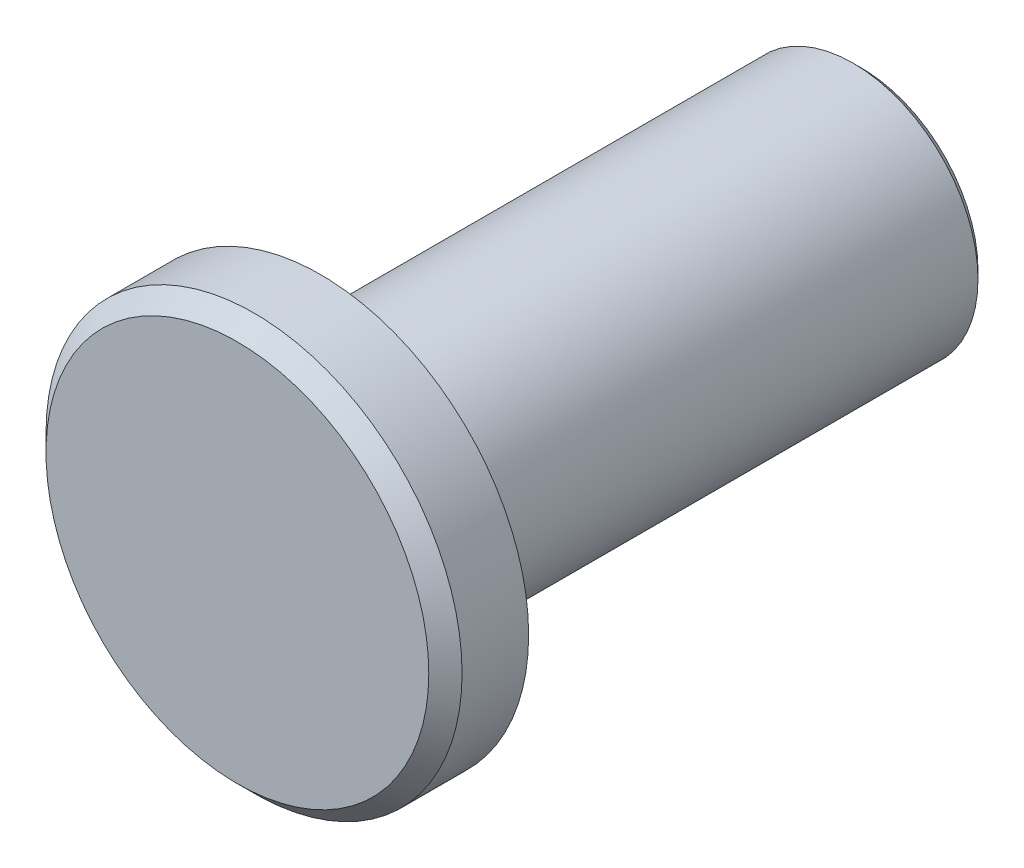
SolidWorks part; units mm, degrees
material "Brass"
ref_plane "Front Plane" through (0, 0, 0) normal (0, 0, 1) x (1, 0, 0)
ref_plane "Top Plane" through (0, 0, 0) normal (0, 1, 0) x (1, 0, 0)
ref_plane "Right Plane" through (0, 0, 0) normal (1, 0, 0) x (0, 0, -1)
sketch "Sketch1" plane through (0, 0, 0) normal (0, 0, 1) x (1, 0, 0)
  circle A0 centre (0, 0) radius 1.5
  dimension "D1" = 3
extrude "Boss-Extrude1" add sketch "Sketch1" along normal blind 6.5
chamfer "Chamfer1" distance 0.1 angle 45 1 edges at (1.5, 0, 0)
sketch "Sketch2" plane through (0, 0, 6.5) normal (0, 0, 1) x (1, 0, 0)
  circle A0 centre (0, 0) radius 2.5
  dimension "D1" = 5
extrude "Boss-Extrude2" add sketch "Sketch2" along normal blind 1
chamfer "Chamfer2" distance 0.2 angle 45 1 edges at (2.5, 0, 7.5)
